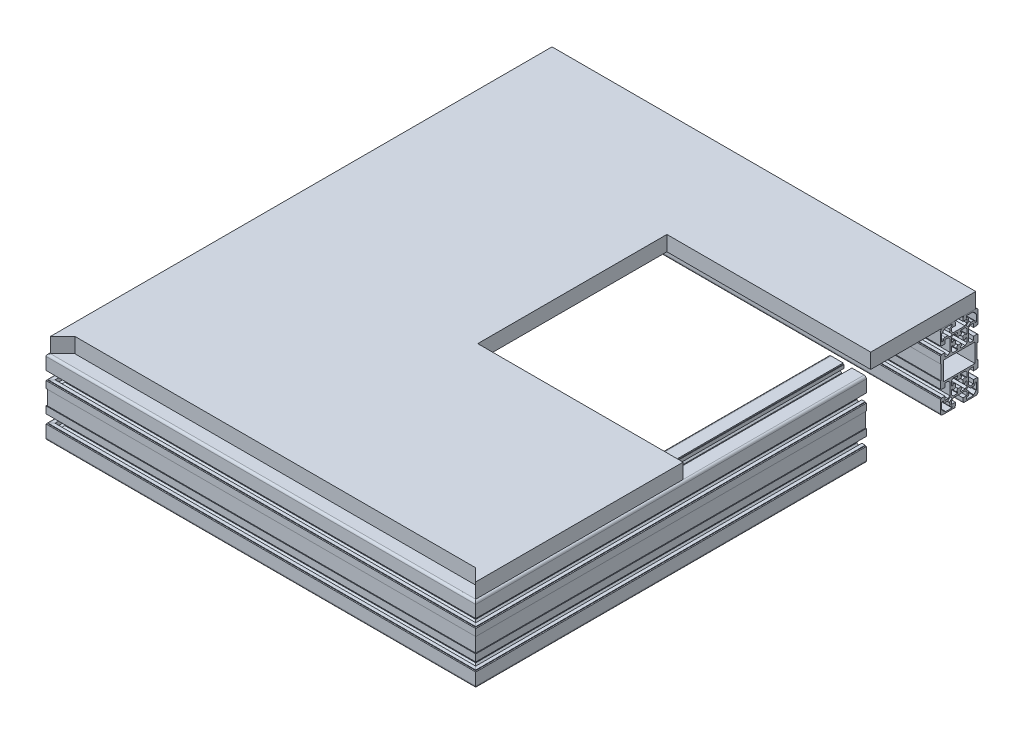
SolidWorks part; units mm, degrees
material "1060 Alloy"
ref_plane "Plano frontal" through (0, 0, 0) normal (0, 0, 1) x (1, 0, 0)
ref_plane "Plano superior" through (0, 0, 0) normal (0, 1, 0) x (1, 0, 0)
ref_plane "Plano direito" through (0, 0, 0) normal (1, 0, 0) x (0, 0, -1)
sketch3d "3DSketch2"
  line L0 (-22873.8611, 5392.1688, 40199.9002) -> (-22853.8611, 5392.1688, 40199.9002) construction
  line L1 (-23395.3248, 5392.1688, 40694.339) -> (-23395.3248, 5392.1688, 40071.4489)
  line L2 (-23395.3248, 5392.1688, 40071.4489) -> (-22853.8611, 5392.1688, 40071.4489)
  line L4 (-23395.3248, 5392.1688, 40694.339) -> (-22873.8611, 5392.1688, 40694.339)
  line L5 (-22873.8611, 5392.1688, 40694.339) -> (-22873.8611, 5392.1688, 40199.9002)
  line L6 (-22853.8611, 5392.1688, 40199.9002) -> (-22853.8611, 5392.1688, 40189.1002) construction
  line L7 (-22853.8611, 5392.1688, 40189.1002) -> (-22853.8611, 5386.9119, 40189.1002) construction
  point P4 (-23399.9269, 5392.1688, 40114.8572)
  point P7 (-23395.3248, 5392.1688, 40046.4489)
  dimension "D4" = 20
other "Aluminium profile 50x100 50X100(1)"
ref_plane "Plane1" through (-22873.8611, 5392.1688, 40694.339) normal (0, 0, -1) x (1, 0, 0)
sketch "Sketch1" plane through (-22873.8611, 5392.1688, 40694.339) normal (0, 0, -1) x (1, 0, 0)
  line L0 (15.1906, 37.8447) -> (11.8847, 34.5389)
  line L1 (11.8847, 34.5389) -> (9.5389, 36.8847)
  line L2 (9.5389, 36.8847) -> (12.8447, 40.1906)
  line L3 (11.2262, 45.7) -> (9.5, 45.7)
  line L4 (9.5, 45.7) -> (9.5, 48.3)
  line L5 (9.5, 48.3) -> (19, 48.3)
  line L6 (19, 48.3) -> (19, 47.2697)
  line L7 (22.2697, 44) -> (23.3, 44)
  line L8 (23.3, 44) -> (23.3, 34.5)
  line L9 (23.3, 34.5) -> (20.7, 34.5)
  line L10 (20.7, 34.5) -> (20.7, 36.2262)
  line L11 (12.8447, -40.1906) -> (9.5389, -36.8847)
  line L12 (9.5389, -36.8847) -> (11.8847, -34.5389)
  line L13 (11.8847, -34.5389) -> (15.1906, -37.8447)
  line L14 (20.7, -36.2262) -> (20.7, -34.5)
  line L15 (20.7, -34.5) -> (23.3, -34.5)
  line L16 (23.3, -34.5) -> (23.3, -44)
  line L17 (23.3, -44) -> (22.2697, -44)
  line L18 (19, -47.2697) -> (19, -48.3)
  line L19 (19, -48.3) -> (9.5, -48.3)
  line L20 (9.5, -48.3) -> (9.5, -45.7)
  line L21 (9.5, -45.7) -> (11.2262, -45.7)
  line L22 (-19, 48.3) -> (-9.5, 48.3)
  line L23 (-9.5, 48.3) -> (-9.5, 45.7)
  line L24 (-9.5, 45.7) -> (-11.2262, 45.7)
  line L25 (-12.8447, 40.1906) -> (-9.5389, 36.8847)
  line L26 (-9.5389, 36.8847) -> (-11.8847, 34.5389)
  line L27 (-11.8847, 34.5389) -> (-15.1906, 37.8447)
  line L28 (-20.7, 36.2262) -> (-20.7, 34.5)
  line L29 (-20.7, 34.5) -> (-23.3, 34.5)
  line L30 (-23.3, 34.5) -> (-23.3, 44)
  line L31 (-23.3, 44) -> (-22.2697, 44)
  line L32 (-19, 47.2697) -> (-19, 48.3)
  line L33 (-23.3, -34.5) -> (-20.7, -34.5)
  line L34 (-20.7, -34.5) -> (-20.7, -36.2262)
  line L35 (-15.1906, -37.8447) -> (-11.8847, -34.5389)
  line L36 (-11.8847, -34.5389) -> (-9.5389, -36.8847)
  line L37 (-9.5389, -36.8847) -> (-12.8447, -40.1906)
  line L38 (-11.2262, -45.7) -> (-9.5, -45.7)
  line L39 (-9.5, -45.7) -> (-9.5, -48.3)
  line L40 (-9.5, -48.3) -> (-19, -48.3)
  line L41 (-19, -48.3) -> (-19, -47.2697)
  line L42 (-22.2697, -44) -> (-23.3, -44)
  line L43 (-23.3, -44) -> (-23.3, -34.5)
  line L44 (-10.3, -23) -> (-10.3, -16.9877)
  line L45 (-10.3, -16.9877) -> (-8.0123, -14.7)
  line L46 (-8.0123, -14.7) -> (-2, -14.7)
  line L47 (-2, -14.7) -> (-2, -16.5539)
  line L48 (-2, -16.5539) -> (-3.5923, -17.2964)
  line L49 (-3.5923, -17.2964) -> (-2.1131, -20.4685)
  line L50 (2.1131, -20.4685) -> (3.5923, -17.2964)
  line L51 (3.5923, -17.2964) -> (2, -16.5539)
  line L52 (2, -16.5539) -> (2, -14.7)
  line L53 (2, -14.7) -> (8.0123, -14.7)
  line L54 (8.0123, -14.7) -> (10.3, -16.9877)
  line L55 (10.3, -16.9877) -> (10.3, -23)
  line L56 (10.3, -23) -> (8.4461, -23)
  line L57 (8.4461, -23) -> (7.7036, -21.4077)
  line L58 (7.7036, -21.4077) -> (4.5315, -22.8869)
  line L59 (4.5315, -27.1131) -> (7.7036, -28.5923)
  line L60 (7.7036, -28.5923) -> (8.4461, -27)
  line L61 (8.4461, -27) -> (10.3, -27)
  line L62 (10.3, -27) -> (10.3, -33.0123)
  line L63 (10.3, -33.0123) -> (8.0123, -35.3)
  line L64 (8.0123, -35.3) -> (2, -35.3)
  line L65 (2, -35.3) -> (2, -33.4461)
  line L66 (2, -33.4461) -> (3.5923, -32.7036)
  line L67 (3.5923, -32.7036) -> (2.1131, -29.5315)
  line L68 (-2.1131, -29.5315) -> (-3.5923, -32.7036)
  line L69 (-3.5923, -32.7036) -> (-2, -33.4461)
  line L70 (-2, -33.4461) -> (-2, -35.3)
  line L71 (-2, -35.3) -> (-8.0123, -35.3)
  line L72 (-8.0123, -35.3) -> (-10.3, -33.0123)
  line L73 (-10.3, -33.0123) -> (-10.3, -27)
  line L74 (-10.3, -27) -> (-8.4461, -27)
  line L75 (-8.4461, -27) -> (-7.7036, -28.5923)
  line L76 (-7.7036, -28.5923) -> (-4.5315, -27.1131)
  line L77 (-4.5315, -22.8869) -> (-7.7036, -21.4077)
  line L78 (-7.7036, -21.4077) -> (-8.4461, -23)
  line L79 (-8.4461, -23) -> (-10.3, -23)
  line L80 (8.0123, 35.3) -> (10.3, 33.0123)
  line L81 (10.3, 33.0123) -> (10.3, 27)
  line L82 (10.3, 27) -> (8.4461, 27)
  line L83 (8.4461, 27) -> (7.7036, 28.5923)
  line L84 (7.7036, 28.5923) -> (4.5315, 27.1131)
  line L85 (4.5315, 22.8869) -> (7.7036, 21.4077)
  line L86 (7.7036, 21.4077) -> (8.4461, 23)
  line L87 (8.4461, 23) -> (10.3, 23)
  line L88 (10.3, 23) -> (10.3, 16.9877)
  line L89 (10.3, 16.9877) -> (8.0123, 14.7)
  line L90 (8.0123, 14.7) -> (2, 14.7)
  line L91 (2, 14.7) -> (2, 16.5539)
  line L92 (2, 16.5539) -> (3.5923, 17.2964)
  line L93 (3.5923, 17.2964) -> (2.1131, 20.4685)
  line L94 (-2.1131, 20.4685) -> (-3.5923, 17.2964)
  line L95 (-3.5923, 17.2964) -> (-2, 16.5539)
  line L96 (-2, 16.5539) -> (-2, 14.7)
  line L97 (-2, 14.7) -> (-8.0123, 14.7)
  line L98 (-8.0123, 14.7) -> (-10.3, 16.9877)
  line L99 (-10.3, 16.9877) -> (-10.3, 23)
  line L100 (-10.3, 23) -> (-8.4461, 23)
  line L101 (-8.4461, 23) -> (-7.7036, 21.4077)
  line L102 (-7.7036, 21.4077) -> (-4.5315, 22.8869)
  line L103 (-4.5315, 27.1131) -> (-7.7036, 28.5923)
  line L104 (-7.7036, 28.5923) -> (-8.4461, 27)
  line L105 (-8.4461, 27) -> (-10.3, 27)
  line L106 (-10.3, 27) -> (-10.3, 33.0123)
  line L107 (-10.3, 33.0123) -> (-8.0123, 35.3)
  line L108 (-8.0123, 35.3) -> (-2, 35.3)
  line L109 (-2, 35.3) -> (-2, 33.4461)
  line L110 (-2, 33.4461) -> (-3.5923, 32.7036)
  line L111 (-3.5923, 32.7036) -> (-2.1131, 29.5315)
  line L112 (2.1131, 29.5315) -> (3.5923, 32.7036)
  line L113 (3.5923, 32.7036) -> (2, 33.4461)
  line L114 (2, 33.4461) -> (2, 35.3)
  line L115 (2, 35.3) -> (8.0123, 35.3)
  line L116 (21, 12.45) -> (21, -12.45)
  line L117 (21, -12.45) -> (-21, -12.45)
  line L118 (-21, -12.45) -> (-21, 12.45)
  line L119 (-21, 12.45) -> (21, 12.45)
  line L120 (23.5, -30) -> (19, -30)
  line L121 (19, -30) -> (19, -35.05)
  line L122 (19, -35.05) -> (14.8, -35.05)
  line L123 (14.8, -35.05) -> (12.5, -32.75)
  line L124 (12.5, -32.75) -> (12.5, -17.25)
  line L125 (12.5, -17.25) -> (14.8, -14.95)
  line L126 (14.8, -14.95) -> (19, -14.95)
  line L127 (19, -14.95) -> (19, -20)
  line L128 (19, -20) -> (23.5, -20)
  line L129 (23.5, -20) -> (23.5, -19.2)
  line L130 (23.5, -19.2) -> (25, -19.2)
  line L131 (25, -19.2) -> (25, -10)
  line L132 (25, -10) -> (24, -10)
  line L133 (24, -10) -> (24, 10)
  line L134 (24, 10) -> (25, 10)
  line L135 (25, 10) -> (25, 19.2)
  line L136 (25, 19.2) -> (23.5, 19.2)
  line L137 (23.5, 19.2) -> (23.5, 20)
  line L138 (23.5, 20) -> (19, 20)
  line L139 (19, 20) -> (19, 14.95)
  line L140 (19, 14.95) -> (14.8, 14.95)
  line L141 (14.8, 14.95) -> (12.5, 17.25)
  line L142 (12.5, 17.25) -> (12.5, 32.75)
  line L143 (12.5, 32.75) -> (14.8, 35.05)
  line L144 (14.8, 35.05) -> (19, 35.05)
  line L145 (19, 35.05) -> (19, 30)
  line L146 (19, 30) -> (23.5, 30)
  line L147 (23.5, 30) -> (23.5, 30.8)
  line L148 (23.5, 30.8) -> (25, 30.8)
  line L149 (25, 30.8) -> (25, 47)
  line L150 (22, 50) -> (5.8, 50)
  line L151 (5.8, 50) -> (5.8, 48.5)
  line L152 (5.8, 48.5) -> (5, 48.5)
  line L153 (5, 48.5) -> (5, 44)
  line L154 (5, 44) -> (10.05, 44)
  line L155 (10.05, 44) -> (10.05, 39.8)
  line L156 (10.05, 39.8) -> (7.75, 37.5)
  line L157 (7.75, 37.5) -> (-7.75, 37.5)
  line L158 (-7.75, 37.5) -> (-10.05, 39.8)
  line L159 (-10.05, 39.8) -> (-10.05, 44)
  line L160 (-10.05, 44) -> (-5, 44)
  line L161 (-5, 44) -> (-5, 48.5)
  line L162 (-5, 48.5) -> (-5.8, 48.5)
  line L163 (-5.8, 48.5) -> (-5.8, 50)
  line L164 (-5.8, 50) -> (-22, 50)
  line L165 (-25, 47) -> (-25, 30.8)
  line L166 (-25, 30.8) -> (-23.5, 30.8)
  line L167 (-23.5, 30.8) -> (-23.5, 30)
  line L168 (-23.5, 30) -> (-19, 30)
  line L169 (-19, 30) -> (-19, 35.05)
  line L170 (-19, 35.05) -> (-14.8, 35.05)
  line L171 (-14.8, 35.05) -> (-12.5, 32.75)
  line L172 (-12.5, 32.75) -> (-12.5, 17.25)
  line L173 (-12.5, 17.25) -> (-14.8, 14.95)
  line L174 (-14.8, 14.95) -> (-19, 14.95)
  line L175 (-19, 14.95) -> (-19, 20)
  line L176 (-19, 20) -> (-23.5, 20)
  line L177 (-23.5, 20) -> (-23.5, 19.2)
  line L178 (-23.5, 19.2) -> (-25, 19.2)
  line L179 (-25, 19.2) -> (-25, 10)
  line L180 (-25, 10) -> (-24, 10)
  line L181 (-24, 10) -> (-24, -10)
  line L182 (-24, -10) -> (-25, -10)
  line L183 (-25, -10) -> (-25, -19.2)
  line L184 (-25, -19.2) -> (-23.5, -19.2)
  line L185 (-23.5, -19.2) -> (-23.5, -20)
  line L186 (-23.5, -20) -> (-19, -20)
  line L187 (-19, -20) -> (-19, -14.95)
  line L188 (-19, -14.95) -> (-14.8, -14.95)
  line L189 (-14.8, -14.95) -> (-12.5, -17.25)
  line L190 (-12.5, -17.25) -> (-12.5, -32.75)
  line L191 (-12.5, -32.75) -> (-14.8, -35.05)
  line L192 (-14.8, -35.05) -> (-19, -35.05)
  line L193 (-19, -35.05) -> (-19, -30)
  line L194 (-19, -30) -> (-23.5, -30)
  line L195 (-23.5, -30) -> (-23.5, -30.8)
  line L196 (-23.5, -30.8) -> (-25, -30.8)
  line L197 (-25, -30.8) -> (-25, -47)
  line L198 (-22, -50) -> (-5.8, -50)
  line L199 (-5.8, -50) -> (-5.8, -48.5)
  line L200 (-5.8, -48.5) -> (-5, -48.5)
  line L201 (-5, -48.5) -> (-5, -44)
  line L202 (-5, -44) -> (-10.05, -44)
  line L203 (-10.05, -44) -> (-10.05, -39.8)
  line L204 (-10.05, -39.8) -> (-7.75, -37.5)
  line L205 (-7.75, -37.5) -> (7.75, -37.5)
  line L206 (7.75, -37.5) -> (10.05, -39.8)
  line L207 (10.05, -39.8) -> (10.05, -44)
  line L208 (10.05, -44) -> (5, -44)
  line L209 (5, -44) -> (5, -48.5)
  line L210 (5, -48.5) -> (5.8, -48.5)
  line L211 (5.8, -48.5) -> (5.8, -50)
  line L212 (5.8, -50) -> (22, -50)
  line L213 (25, -47) -> (25, -30.8)
  line L214 (25, -30.8) -> (23.5, -30.8)
  line L215 (23.5, -30.8) -> (23.5, -30)
  arc A0 (15.5214, 37.9081) -> (15.1906, 37.8447) centre (15.4027, 37.6326) ccw
  arc A1 (12.8447, 40.1906) -> (12.9081, 40.5214) centre (12.6326, 40.4027) ccw
  arc A2 (12.9081, 40.5214) -> (12.674, 43.8077) centre (17.5, 42.5) cw
  arc A3 (12.674, 43.8077) -> (11.2262, 45.7) centre (11.2262, 44.2) ccw
  arc A4 (19, 47.2697) -> (22.2697, 44) centre (17.5, 42.5) cw
  arc A5 (20.7, 36.2262) -> (18.8077, 37.674) centre (19.2, 36.2262) ccw
  arc A6 (18.8077, 37.674) -> (15.5214, 37.9081) centre (17.5, 42.5) cw
  arc A7 (15.1906, -37.8447) -> (15.5214, -37.9081) centre (15.4027, -37.6326) ccw
  arc A8 (15.5214, -37.9081) -> (18.8077, -37.674) centre (17.5, -42.5) cw
  arc A9 (18.8077, -37.674) -> (20.7, -36.2262) centre (19.2, -36.2262) ccw
  arc A10 (22.2697, -44) -> (19, -47.2697) centre (17.5, -42.5) cw
  arc A11 (11.2262, -45.7) -> (12.674, -43.8077) centre (11.2262, -44.2) ccw
  arc A12 (12.674, -43.8077) -> (12.9081, -40.5214) centre (17.5, -42.5) cw
  arc A13 (12.9081, -40.5214) -> (12.8447, -40.1906) centre (12.6326, -40.4027) ccw
  arc A14 (-11.2262, 45.7) -> (-12.674, 43.8077) centre (-11.2262, 44.2) ccw
  arc A15 (-12.674, 43.8077) -> (-12.9081, 40.5214) centre (-17.5, 42.5) cw
  arc A16 (-12.9081, 40.5214) -> (-12.8447, 40.1906) centre (-12.6326, 40.4027) ccw
  arc A17 (-15.1906, 37.8447) -> (-15.5214, 37.9081) centre (-15.4027, 37.6326) ccw
  arc A18 (-15.5214, 37.9081) -> (-18.8077, 37.674) centre (-17.5, 42.5) cw
  arc A19 (-18.8077, 37.674) -> (-20.7, 36.2262) centre (-19.2, 36.2262) ccw
  arc A20 (-22.2697, 44) -> (-19, 47.2697) centre (-17.5, 42.5) cw
  arc A21 (-20.7, -36.2262) -> (-18.8077, -37.674) centre (-19.2, -36.2262) ccw
  arc A22 (-18.8077, -37.674) -> (-15.5214, -37.9081) centre (-17.5, -42.5) cw
  arc A23 (-15.5214, -37.9081) -> (-15.1906, -37.8447) centre (-15.4027, -37.6326) ccw
  arc A24 (-12.8447, -40.1906) -> (-12.9081, -40.5214) centre (-12.6326, -40.4027) ccw
  arc A25 (-12.9081, -40.5214) -> (-12.674, -43.8077) centre (-17.5, -42.5) cw
  arc A26 (-12.674, -43.8077) -> (-11.2262, -45.7) centre (-11.2262, -44.2) ccw
  arc A27 (-19, -47.2697) -> (-22.2697, -44) centre (-17.5, -42.5) cw
  arc A28 (-2.1131, -20.4685) -> (2.1131, -20.4685) centre (0, -25) cw
  arc A29 (4.5315, -22.8869) -> (4.5315, -27.1131) centre (0, -25) cw
  arc A30 (2.1131, -29.5315) -> (-2.1131, -29.5315) centre (0, -25) cw
  arc A31 (-4.5315, -27.1131) -> (-4.5315, -22.8869) centre (0, -25) cw
  arc A32 (4.5315, 27.1131) -> (4.5315, 22.8869) centre (0, 25) cw
  arc A33 (2.1131, 20.4685) -> (-2.1131, 20.4685) centre (0, 25) cw
  arc A34 (-4.5315, 22.8869) -> (-4.5315, 27.1131) centre (0, 25) cw
  arc A35 (-2.1131, 29.5315) -> (2.1131, 29.5315) centre (0, 25) cw
  arc A36 (25, 47) -> (22, 50) centre (22, 47) ccw
  arc A37 (-22, 50) -> (-25, 47) centre (-22, 47) ccw
  arc A38 (-25, -47) -> (-22, -50) centre (-22, -47) ccw
  arc A39 (22, -50) -> (25, -47) centre (22, -47) ccw
  point P282 (0, 0)
sketch "Sketch2" plane through (0, 5442.1688, 0) normal (0, 1, 0) x (1, 0, 0)
  line L1 (-23417.3248, -40719.339) -> (-23124.9194, -40719.339)
  line L2 (-23417.3248, -40719.339) -> (-23417.3248, -40049.4489)
  line L3 (-23417.3248, -40049.4489) -> (-23124.9194, -40049.4489)
  line L4 (-23124.9194, -40719.339) -> (-23124.9194, -40049.4489)
  line L5 (-23417.3248, -40716.339) -> (-23417.3248, -40049.4489) construction
  line L6 (-23417.3248, -40049.4489) -> (-22853.8611, -40049.4489) construction
  line L7 (-22848.8611, -40719.339) -> (-23420.3248, -40719.339) construction
  line L8 (-22851.8611, -40199.9002) -> (-22851.8611, -40716.339) construction
  line L9 (-23124.9194, -40049.4489) -> (-22853.8611, -40049.4489)
  line L10 (-23124.9194, -40049.4489) -> (-23124.9194, -40189.1002)
  line L11 (-23124.9194, -40189.1002) -> (-22853.8611, -40189.1002)
  line L12 (-22853.8611, -40049.4489) -> (-22853.8611, -40189.1002)
  line L13 (-23124.9194, -40719.339) -> (-22851.8611, -40719.339)
  line L14 (-23124.9194, -40719.339) -> (-23124.9194, -40440.6089)
  line L15 (-23124.9194, -40440.6089) -> (-22851.8611, -40440.6089)
  line L16 (-22851.8611, -40719.339) -> (-22851.8611, -40440.6089)
  line L17 (-22853.8611, -40047.9002) -> (-22853.8611, -40179.1002) construction
  line L18 (-22868.8611, -40189.1002) -> (-22953.8611, -40189.1002) construction
  point P18 (-22853.8611, -40172.0962)
extrude "Boss-Extrude1" add sketch "Sketch2" along normal blind 20 separate body contours L16 L15 L4 M7 M8 | L4 L3 L2 M8 M5 | L12 L9 L4 L11
sketch "Sketch3" plane through (0, 5462.1688, 0) normal (0, 1, 0) x (1, 0, 0)
  line L0 (-23313.9697, -40111.1916) -> (-23138.9697, -40111.1916) construction
  line L1 (-22944.3788, -40697.8857) -> (-22944.3788, -40467.8857) construction
  line L2 (-23313.9697, -40101.1916) -> (-23138.9697, -40101.1916)
  line L3 (-23313.9697, -40121.1916) -> (-23138.9697, -40121.1916)
  line L4 (-23313.9697, -40111.1916) -> (-23313.9697, -40561.1916) construction
  line L5 (-23303.9697, -40111.1916) -> (-23303.9697, -40561.1916)
  line L6 (-23323.9697, -40111.1916) -> (-23323.9697, -40561.1916)
  line L7 (-23313.9697, -40561.1916) -> (-22863.9697, -40561.1916) construction
  line L8 (-23313.9697, -40551.1916) -> (-22863.9697, -40551.1916)
  line L9 (-23313.9697, -40571.1916) -> (-22863.9697, -40571.1916)
  arc A0 (-23313.9697, -40101.1916) -> (-23313.9697, -40121.1916) centre (-23313.9697, -40111.1916) ccw
  arc A1 (-23138.9697, -40121.1916) -> (-23138.9697, -40101.1916) centre (-23138.9697, -40111.1916) ccw
  arc A2 (-23303.9697, -40111.1916) -> (-23323.9697, -40111.1916) centre (-23313.9697, -40111.1916) ccw
  arc A3 (-23323.9697, -40561.1916) -> (-23303.9697, -40561.1916) centre (-23313.9697, -40561.1916) ccw
  arc A4 (-23313.9697, -40551.1916) -> (-23313.9697, -40571.1916) centre (-23313.9697, -40561.1916) ccw
  arc A5 (-22863.9697, -40571.1916) -> (-22863.9697, -40551.1916) centre (-22863.9697, -40561.1916) ccw
  point P4 (-23226.4697, -40111.1916)
  point P9 (-23313.9697, -40336.1916)
  point P18 (-23088.9697, -40561.1916)
  point P23 (0, 0)
  point P24 (-23367.5718, -40423.5306)
  point P25 (0, 0)
  point P26 (0, 0)
  point P27 (0, 0)
  dimension "D1" = 10
  dimension "D2" = 10
  dimension "D3" = 10
  dimension "D4" = 450
  dimension "D5" = 450
  dimension "D6" = 175
